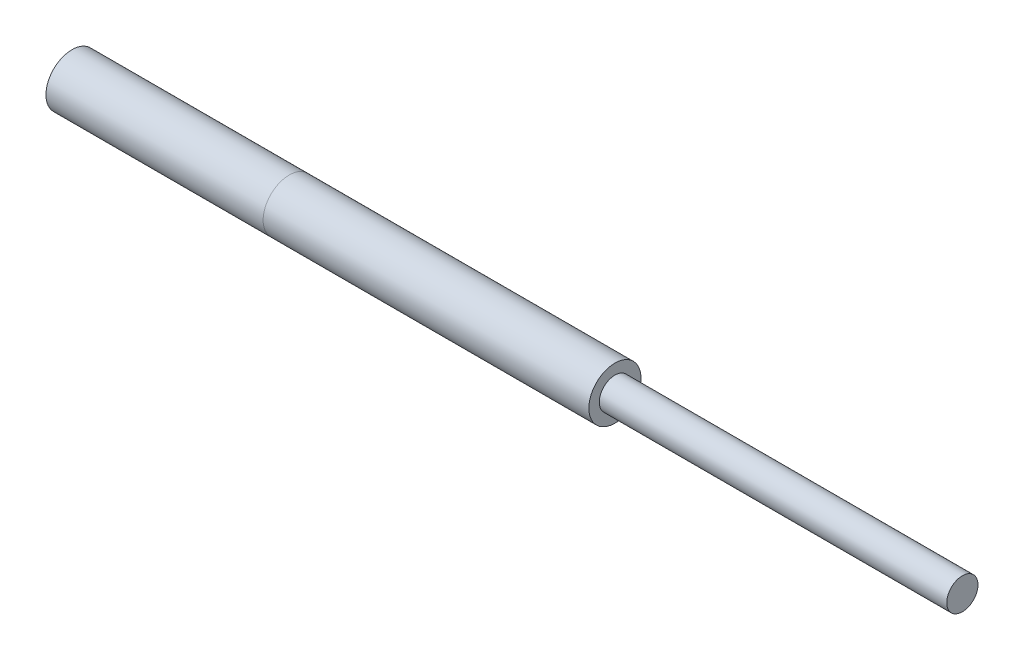
SolidWorks part; units mm, degrees
ref_plane "Front Plane" through (0, 0, 0) normal (0, 0, 1) x (1, 0, 0)
ref_plane "Top Plane" through (0, 0, 0) normal (0, 1, 0) x (1, 0, 0)
ref_plane "Right Plane" through (0, 0, 0) normal (1, 0, 0) x (0, 0, -1)
sketch "Sketch1" plane through (0, 0, 0) normal (1, 0, 0) x (0, 0, -1)
  circle A0 centre (0, 0) radius 20
  circle A1 centre (0, 0) radius 30
  dimension "D1" = 40
  dimension "D2" = 60
extrude "Boss-Extrude1" add sketch "Sketch1" along normal blind 250
sketch "Sketch3" plane through (250, 0, 0) normal (1, 0, 0) x (0, 0, -1)
  circle A0 centre (0, 0) radius 30
  dimension "D1" = 60
extrude "Boss-Extrude2" add sketch "Sketch3" along normal blind 375 separate body
sketch "Sketch4" plane through (625, 0, 0) normal (1, 0, 0) x (0, 0, -1)
  circle A0 centre (0, 0) radius 18
  dimension "D1" = 36
extrude "Boss-Extrude3" add sketch "Sketch4" along normal blind 400 separate body
